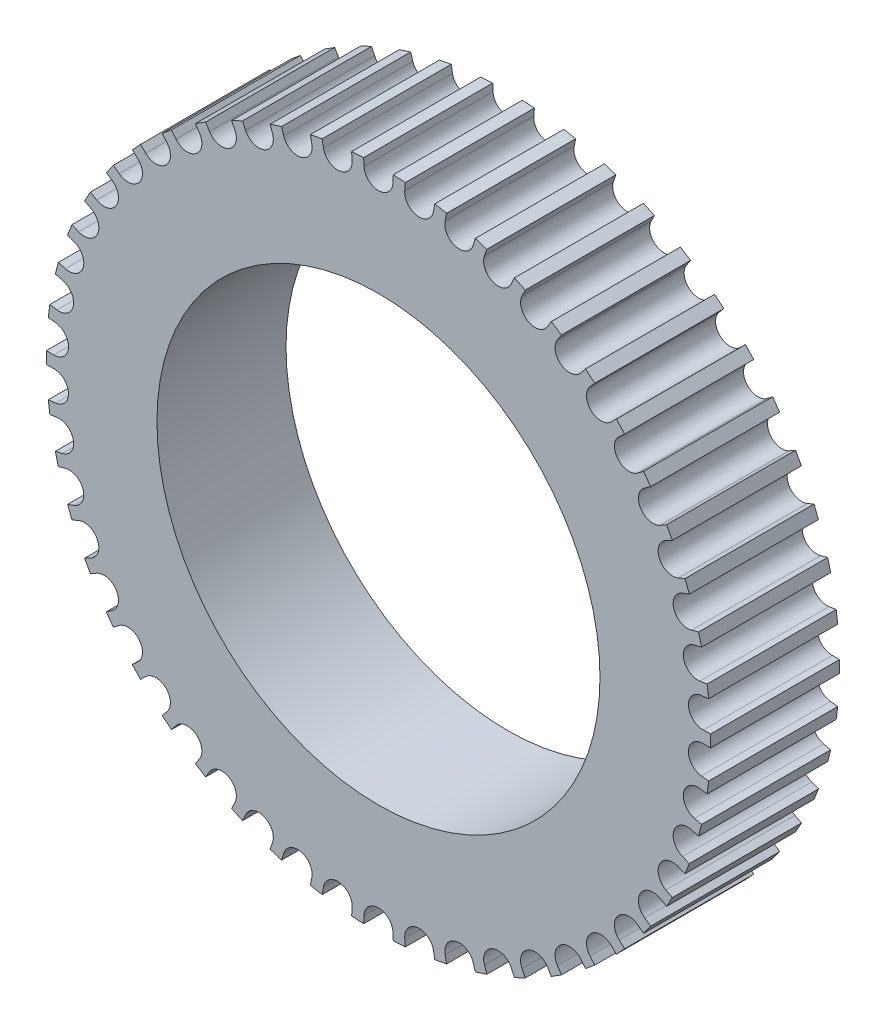
SolidWorks part; units mm, degrees
ref_plane "Front" through (0, 0, 0) normal (0, 0, 1) x (1, 0, 0)
ref_plane "Top" through (0, 0, 0) normal (0, 1, 0) x (1, 0, 0)
ref_plane "Right" through (0, 0, 0) normal (1, 0, 0) x (0, 0, -1)
sketch "Sketch1" plane through (0, 0, 0) normal (0, 0, 1) x (1, 0, 0)
  line L30 (-0.6744, -15.0836) -> (-0.6892, -15.4226)
  line L31 (0.6744, -15.0836) -> (0.6892, -15.4226)
  line L32 (0, -14.438) -> (0, -15.438) construction
  line L33 (-0.6892, -15.4226) -> (-1.2492, -15.3874)
  line L34 (-2.5595, -14.8801) -> (-2.6167, -15.2147)
  line L35 (-1.2214, -15.0492) -> (-1.2492, -15.3874)
  line L36 (-2.6167, -15.2147) -> (-3.1679, -15.1095)
  line L37 (-1.8096, -14.3242) -> (-1.9349, -15.3163) construction
  line L38 (-4.4043, -14.442) -> (-4.503, -14.7667)
  line L39 (-3.098, -14.7774) -> (-3.1679, -15.1095)
  line L40 (-4.503, -14.7667) -> (-5.0367, -14.5933)
  line L41 (-3.5906, -13.9844) -> (-3.8393, -14.953) construction
  line L42 (-6.1796, -13.7761) -> (-6.3182, -14.0859)
  line L43 (-4.9256, -14.2726) -> (-5.0367, -14.5933)
  line L44 (-6.3182, -14.0859) -> (-6.826, -13.847)
  line L45 (-5.315, -13.4241) -> (-5.6831, -14.3539) construction
  line L46 (-7.8575, -12.893) -> (-8.0338, -13.183)
  line L47 (-6.6756, -13.5427) -> (-6.826, -13.847)
  line L48 (-8.0338, -13.183) -> (-8.5077, -12.8823)
  line L49 (-6.9556, -12.6521) -> (-7.4373, -13.5284) construction
  line L50 (-9.4115, -11.8065) -> (-9.6227, -12.0721)
  line L51 (-8.3203, -12.5993) -> (-8.5077, -12.8823)
  line L52 (-9.6227, -12.0721) -> (-10.0551, -11.7144)
  line L53 (-8.4865, -11.6806) -> (-9.0742, -12.4896) construction
  line L54 (-10.817, -10.5338) -> (-11.0599, -10.7709)
  line L55 (-9.8338, -11.4571) -> (-10.0551, -11.7144)
  line L56 (-11.0599, -10.7709) -> (-11.4441, -10.3618)
  line L57 (-9.8835, -10.5249) -> (-10.5681, -11.2538) construction
  line L58 (-12.052, -9.095) -> (-12.3226, -9.2998)
  line L59 (-11.1923, -10.1342) -> (-11.4441, -10.3618)
  line L60 (-12.3226, -9.2998) -> (-12.6525, -8.8457)
  line L61 (-11.1247, -9.2031) -> (-11.8952, -9.8406) construction
  line L62 (-13.0968, -7.5128) -> (-13.391, -7.682)
  line L63 (-12.3742, -8.6516) -> (-12.6525, -8.8457)
  line L64 (-13.391, -7.682) -> (-13.6614, -7.1902)
  line L65 (-12.1904, -7.7363) -> (-13.0348, -8.2721) construction
  line L66 (-13.9352, -5.8121) -> (-14.2483, -5.9431)
  line L67 (-13.3609, -7.0325) -> (-13.6614, -7.1902)
  line L68 (-14.2483, -5.9431) -> (-14.4548, -5.4213)
  line L69 (-13.0639, -6.1474) -> (-13.9687, -6.5732) construction
  line L70 (-14.5537, -4.0197) -> (-14.8808, -4.1104)
  line L71 (-14.137, -5.3024) -> (-14.4548, -5.4213)
  line L72 (-14.8808, -4.1104) -> (-15.0203, -3.5669)
  line L73 (-13.7314, -4.4616) -> (-14.6824, -4.7706) construction
  line L74 (-14.9428, -2.164) -> (-15.2786, -2.213)
  line L75 (-14.6901, -3.4888) -> (-15.0203, -3.5669)
  line L76 (-15.2786, -2.213) -> (-15.3489, -1.6562)
  line L77 (-14.1823, -2.7054) -> (-15.1646, -2.8928) construction
  line L78 (-15.0962, -0.2741) -> (-15.4355, -0.2806)
  line L79 (-15.0115, -1.6201) -> (-15.3489, -1.6562)
  line L80 (-15.4355, -0.2806) -> (-15.4355, 0.2806)
  line L81 (-14.4095, -0.9066) -> (-15.4076, -0.9694) construction
  line L82 (-15.0115, 1.6201) -> (-15.3489, 1.6562)
  line L83 (-15.0962, 0.2741) -> (-15.4355, 0.2806)
  line L84 (-15.3489, 1.6562) -> (-15.2786, 2.213)
  line L85 (-14.4095, 0.9066) -> (-15.4076, 0.9694) construction
  line L86 (-14.6901, 3.4888) -> (-15.0203, 3.5669)
  line L87 (-14.9428, 2.164) -> (-15.2786, 2.213)
  line L88 (-15.0203, 3.5669) -> (-14.8808, 4.1104)
  line L89 (-14.1823, 2.7054) -> (-15.1646, 2.8928) construction
  line L90 (-14.137, 5.3024) -> (-14.4548, 5.4213)
  line L91 (-14.5537, 4.0197) -> (-14.8808, 4.1104)
  line L92 (-14.4548, 5.4213) -> (-14.2483, 5.9431)
  line L93 (-13.7314, 4.4616) -> (-14.6824, 4.7706) construction
  line L94 (-13.3609, 7.0325) -> (-13.6614, 7.1902)
  line L95 (-13.9352, 5.8121) -> (-14.2483, 5.9431)
  line L96 (-13.6614, 7.1902) -> (-13.391, 7.682)
  line L97 (-13.0639, 6.1474) -> (-13.9687, 6.5732) construction
  line L98 (-12.3742, 8.6516) -> (-12.6525, 8.8457)
  line L99 (-13.0968, 7.5128) -> (-13.391, 7.682)
  line L100 (-12.6525, 8.8457) -> (-12.3226, 9.2998)
  line L101 (-12.1904, 7.7363) -> (-13.0348, 8.2721) construction
  line L102 (-11.1923, 10.1342) -> (-11.4441, 10.3618)
  line L103 (-12.052, 9.095) -> (-12.3226, 9.2998)
  line L104 (-11.4441, 10.3618) -> (-11.0599, 10.7709)
  line L105 (-11.1247, 9.2031) -> (-11.8952, 9.8406) construction
  line L106 (-9.8338, 11.4571) -> (-10.0551, 11.7144)
  line L107 (-10.817, 10.5338) -> (-11.0599, 10.7709)
  line L108 (-10.0551, 11.7144) -> (-9.6227, 12.0721)
  line L109 (-9.8835, 10.5249) -> (-10.5681, 11.2538) construction
  line L110 (-8.3203, 12.5993) -> (-8.5077, 12.8823)
  line L111 (-9.4115, 11.8065) -> (-9.6227, 12.0721)
  line L112 (-8.5077, 12.8823) -> (-8.0338, 13.183)
  line L113 (-8.4865, 11.6806) -> (-9.0742, 12.4896) construction
  line L114 (-6.6756, 13.5427) -> (-6.826, 13.847)
  line L115 (-7.8575, 12.893) -> (-8.0338, 13.183)
  line L116 (-6.826, 13.847) -> (-6.3182, 14.0859)
  line L117 (-6.9556, 12.6521) -> (-7.4373, 13.5284) construction
  line L118 (-4.9256, 14.2726) -> (-5.0367, 14.5933)
  line L119 (-6.1796, 13.7761) -> (-6.3182, 14.0859)
  line L120 (-5.0367, 14.5933) -> (-4.503, 14.7667)
  line L121 (-5.315, 13.4241) -> (-5.6831, 14.3539) construction
  line L122 (-3.098, 14.7774) -> (-3.1679, 15.1095)
  line L123 (-4.4043, 14.442) -> (-4.503, 14.7667)
  line L124 (-3.1679, 15.1095) -> (-2.6167, 15.2147)
  line L125 (-3.5906, 13.9844) -> (-3.8393, 14.953) construction
  line L126 (-1.2214, 15.0492) -> (-1.2492, 15.3874)
  line L127 (-2.5595, 14.8801) -> (-2.6167, 15.2147)
  line L128 (-1.2492, 15.3874) -> (-0.6892, 15.4226)
  line L129 (-1.8096, 14.3242) -> (-1.9349, 15.3163) construction
  line L130 (0.6744, 15.0836) -> (0.6892, 15.4226)
  line L131 (-0.6744, 15.0836) -> (-0.6892, 15.4226)
  line L132 (0.6892, 15.4226) -> (1.2492, 15.3874)
  line L133 (0, 14.438) -> (0, 15.438) construction
  line L134 (2.5595, 14.8801) -> (2.6167, 15.2147)
  line L135 (1.2214, 15.0492) -> (1.2492, 15.3874)
  line L136 (2.6167, 15.2147) -> (3.1679, 15.1095)
  line L137 (1.8096, 14.3242) -> (1.9349, 15.3163) construction
  line L138 (4.4043, 14.442) -> (4.503, 14.7667)
  line L139 (3.098, 14.7774) -> (3.1679, 15.1095)
  line L140 (4.503, 14.7667) -> (5.0367, 14.5933)
  line L141 (3.5906, 13.9844) -> (3.8393, 14.953) construction
  line L142 (6.1796, 13.7761) -> (6.3182, 14.0859)
  line L143 (4.9256, 14.2726) -> (5.0367, 14.5933)
  line L144 (6.3182, 14.0859) -> (6.826, 13.847)
  line L145 (5.315, 13.4241) -> (5.6831, 14.3539) construction
  line L146 (7.8575, 12.893) -> (8.0338, 13.183)
  line L147 (6.6756, 13.5427) -> (6.826, 13.847)
  line L148 (8.0338, 13.183) -> (8.5077, 12.8823)
  line L149 (6.9556, 12.6521) -> (7.4373, 13.5284) construction
  line L150 (0, 0) -> (0, -14.438) construction
  line L151 (9.4115, 11.8065) -> (9.6227, 12.0721)
  line L152 (8.3203, 12.5993) -> (8.5077, 12.8823)
  line L153 (9.6227, 12.0721) -> (10.0551, 11.7144)
  line L154 (8.4865, 11.6806) -> (9.0742, 12.4896) construction
  line L155 (10.817, 10.5338) -> (11.0599, 10.7709)
  line L156 (9.8338, 11.4571) -> (10.0551, 11.7144)
  line L157 (11.0599, 10.7709) -> (11.4441, 10.3618)
  line L158 (9.8835, 10.5249) -> (10.5681, 11.2538) construction
  line L159 (12.052, 9.095) -> (12.3226, 9.2998)
  line L160 (11.1923, 10.1342) -> (11.4441, 10.3618)
  line L161 (12.3226, 9.2998) -> (12.6525, 8.8457)
  line L162 (11.1247, 9.2031) -> (11.8952, 9.8406) construction
  line L163 (13.0968, 7.5128) -> (13.391, 7.682)
  line L164 (12.3742, 8.6516) -> (12.6525, 8.8457)
  line L165 (13.391, 7.682) -> (13.6614, 7.1902)
  line L166 (12.1904, 7.7363) -> (13.0348, 8.2721) construction
  line L167 (13.9352, 5.8121) -> (14.2483, 5.9431)
  line L168 (13.3609, 7.0325) -> (13.6614, 7.1902)
  line L169 (14.2483, 5.9431) -> (14.4548, 5.4213)
  line L170 (13.0639, 6.1474) -> (13.9687, 6.5732) construction
  line L171 (14.5537, 4.0197) -> (14.8808, 4.1104)
  line L172 (14.137, 5.3024) -> (14.4548, 5.4213)
  line L173 (14.8808, 4.1104) -> (15.0203, 3.5669)
  line L174 (13.7314, 4.4616) -> (14.6824, 4.7706) construction
  line L175 (14.9428, 2.164) -> (15.2786, 2.213)
  line L176 (14.6901, 3.4888) -> (15.0203, 3.5669)
  line L177 (15.2786, 2.213) -> (15.3489, 1.6562)
  line L178 (14.1823, 2.7054) -> (15.1646, 2.8928) construction
  line L179 (15.0962, 0.2741) -> (15.4355, 0.2806)
  line L180 (15.0115, 1.6201) -> (15.3489, 1.6562)
  line L181 (15.4355, 0.2806) -> (15.4355, -0.2806)
  line L182 (14.4095, 0.9066) -> (15.4076, 0.9694) construction
  line L183 (15.0115, -1.6201) -> (15.3489, -1.6562)
  line L184 (15.0962, -0.2741) -> (15.4355, -0.2806)
  line L185 (15.3489, -1.6562) -> (15.2786, -2.213)
  line L186 (14.4095, -0.9066) -> (15.4076, -0.9694) construction
  line L187 (14.6901, -3.4888) -> (15.0203, -3.5669)
  line L188 (14.9428, -2.164) -> (15.2786, -2.213)
  line L189 (15.0203, -3.5669) -> (14.8808, -4.1104)
  line L190 (14.1823, -2.7054) -> (15.1646, -2.8928) construction
  line L191 (14.137, -5.3024) -> (14.4548, -5.4213)
  line L192 (14.5537, -4.0197) -> (14.8808, -4.1104)
  line L193 (14.4548, -5.4213) -> (14.2483, -5.9431)
  line L194 (13.7314, -4.4616) -> (14.6824, -4.7706) construction
  line L195 (13.3609, -7.0325) -> (13.6614, -7.1902)
  line L196 (13.9352, -5.8121) -> (14.2483, -5.9431)
  line L197 (13.6614, -7.1902) -> (13.391, -7.682)
  line L198 (13.0639, -6.1474) -> (13.9687, -6.5732) construction
  line L199 (12.3742, -8.6516) -> (12.6525, -8.8457)
  line L200 (13.0968, -7.5128) -> (13.391, -7.682)
  line L201 (12.6525, -8.8457) -> (12.3226, -9.2998)
  line L202 (12.1904, -7.7363) -> (13.0348, -8.2721) construction
  line L203 (11.1923, -10.1342) -> (11.4441, -10.3618)
  line L204 (12.052, -9.095) -> (12.3226, -9.2998)
  line L205 (11.4441, -10.3618) -> (11.0599, -10.7709)
  line L206 (11.1247, -9.2031) -> (11.8952, -9.8406) construction
  line L207 (9.8338, -11.4571) -> (10.0551, -11.7144)
  line L208 (10.817, -10.5338) -> (11.0599, -10.7709)
  line L209 (10.0551, -11.7144) -> (9.6227, -12.0721)
  line L210 (9.8835, -10.5249) -> (10.5681, -11.2538) construction
  line L211 (8.3203, -12.5993) -> (8.5077, -12.8823)
  line L212 (9.4115, -11.8065) -> (9.6227, -12.0721)
  line L213 (8.5077, -12.8823) -> (8.0338, -13.183)
  line L214 (8.4865, -11.6806) -> (9.0742, -12.4896) construction
  line L215 (6.6756, -13.5427) -> (6.826, -13.847)
  line L216 (7.8575, -12.893) -> (8.0338, -13.183)
  line L217 (6.826, -13.847) -> (6.3182, -14.0859)
  line L218 (6.9556, -12.6521) -> (7.4373, -13.5284) construction
  line L219 (4.9256, -14.2726) -> (5.0367, -14.5933)
  line L220 (6.1796, -13.7761) -> (6.3182, -14.0859)
  line L221 (5.0367, -14.5933) -> (4.503, -14.7667)
  line L222 (5.315, -13.4241) -> (5.6831, -14.3539) construction
  line L223 (3.098, -14.7774) -> (3.1679, -15.1095)
  line L224 (4.4043, -14.442) -> (4.503, -14.7667)
  line L225 (3.1679, -15.1095) -> (2.6167, -15.2147)
  line L226 (3.5906, -13.9844) -> (3.8393, -14.953) construction
  line L227 (1.2214, -15.0492) -> (1.2492, -15.3874)
  line L228 (2.5595, -14.8801) -> (2.6167, -15.2147)
  line L229 (1.2492, -15.3874) -> (0.6892, -15.4226)
  line L230 (1.8096, -14.3242) -> (1.9349, -15.3163) construction
  circle A31 centre (0, 0) radius 15.438 construction
  arc A32 (-0.6744, -15.0836) -> (0.6744, -15.0836) centre (0, -15.113) cw
  arc A33 (-2.5595, -14.8801) -> (-1.2214, -15.0492) centre (-1.8942, -14.9939) cw
  arc A34 (-4.4043, -14.442) -> (-3.098, -14.7774) centre (-3.7585, -14.6382) cw
  arc A35 (-6.1796, -13.7761) -> (-4.9256, -14.2726) centre (-5.5635, -14.0517) cw
  arc A36 (-7.8575, -12.893) -> (-6.6756, -13.5427) centre (-7.2808, -13.2436) cw
  arc A37 (-9.4115, -11.8065) -> (-8.3203, -12.5993) centre (-8.8832, -12.2267) cw
  arc A38 (-10.817, -10.5338) -> (-9.8338, -11.4571) centre (-10.3456, -11.0169) cw
  arc A39 (-12.052, -9.095) -> (-11.1923, -10.1342) centre (-11.6448, -9.6334) cw
  arc A40 (-13.0968, -7.5128) -> (-12.3742, -8.6516) centre (-12.7604, -8.098) cw
  arc A41 (-13.9352, -5.8121) -> (-13.3609, -7.0325) centre (-13.6747, -6.4348) cw
  arc A42 (-14.5537, -4.0197) -> (-14.137, -5.3024) centre (-14.3733, -4.6702) cw
  arc A43 (-14.9428, -2.164) -> (-14.6901, -3.4888) centre (-14.8453, -2.8319) cw
  arc A44 (-15.0962, -0.2741) -> (-15.0115, -1.6201) centre (-15.0832, -0.949) cw
  arc A45 (-15.0115, 1.6201) -> (-15.0962, 0.2741) centre (-15.0832, 0.949) cw
  arc A46 (-14.6901, 3.4888) -> (-14.9428, 2.164) centre (-14.8453, 2.8319) cw
  arc A47 (-14.137, 5.3024) -> (-14.5537, 4.0197) centre (-14.3733, 4.6702) cw
  arc A48 (-13.3609, 7.0325) -> (-13.9352, 5.8121) centre (-13.6747, 6.4348) cw
  arc A49 (-12.3742, 8.6516) -> (-13.0968, 7.5128) centre (-12.7604, 8.098) cw
  arc A50 (-11.1923, 10.1342) -> (-12.052, 9.095) centre (-11.6448, 9.6334) cw
  arc A51 (-9.8338, 11.4571) -> (-10.817, 10.5338) centre (-10.3456, 11.0169) cw
  arc A52 (-8.3203, 12.5993) -> (-9.4115, 11.8065) centre (-8.8832, 12.2267) cw
  arc A53 (-6.6756, 13.5427) -> (-7.8575, 12.893) centre (-7.2808, 13.2436) cw
  arc A54 (-4.9256, 14.2726) -> (-6.1796, 13.7761) centre (-5.5635, 14.0517) cw
  arc A55 (-3.098, 14.7774) -> (-4.4043, 14.442) centre (-3.7585, 14.6382) cw
  arc A56 (-1.2214, 15.0492) -> (-2.5595, 14.8801) centre (-1.8942, 14.9939) cw
  arc A57 (0.6744, 15.0836) -> (-0.6744, 15.0836) centre (0, 15.113) cw
  arc A58 (2.5595, 14.8801) -> (1.2214, 15.0492) centre (1.8942, 14.9939) cw
  arc A59 (4.4043, 14.442) -> (3.098, 14.7774) centre (3.7585, 14.6382) cw
  arc A60 (6.1796, 13.7761) -> (4.9256, 14.2726) centre (5.5635, 14.0517) cw
  arc A61 (7.8575, 12.893) -> (6.6756, 13.5427) centre (7.2808, 13.2436) cw
  arc A62 (9.4115, 11.8065) -> (8.3203, 12.5993) centre (8.8832, 12.2267) cw
  arc A63 (10.817, 10.5338) -> (9.8338, 11.4571) centre (10.3456, 11.0169) cw
  arc A64 (12.052, 9.095) -> (11.1923, 10.1342) centre (11.6448, 9.6334) cw
  arc A65 (13.0968, 7.5128) -> (12.3742, 8.6516) centre (12.7604, 8.098) cw
  arc A66 (13.9352, 5.8121) -> (13.3609, 7.0325) centre (13.6747, 6.4348) cw
  arc A73 (-1.9349, -15.3163) -> (0, -15.438) centre (0, 0) ccw construction
  arc A74 (14.5537, 4.0197) -> (14.137, 5.3024) centre (14.3733, 4.6702) cw
  arc A75 (14.9428, 2.164) -> (14.6901, 3.4888) centre (14.8453, 2.8319) cw
  arc A76 (15.0962, 0.2741) -> (15.0115, 1.6201) centre (15.0832, 0.949) cw
  arc A77 (15.0115, -1.6201) -> (15.0962, -0.2741) centre (15.0832, -0.949) cw
  arc A78 (14.6901, -3.4888) -> (14.9428, -2.164) centre (14.8453, -2.8319) cw
  arc A79 (14.137, -5.3024) -> (14.5537, -4.0197) centre (14.3733, -4.6702) cw
  arc A80 (13.3609, -7.0325) -> (13.9352, -5.8121) centre (13.6747, -6.4348) cw
  arc A81 (12.3742, -8.6516) -> (13.0968, -7.5128) centre (12.7604, -8.098) cw
  arc A82 (11.1923, -10.1342) -> (12.052, -9.095) centre (11.6448, -9.6334) cw
  arc A83 (9.8338, -11.4571) -> (10.817, -10.5338) centre (10.3456, -11.0169) cw
  arc A84 (8.3203, -12.5993) -> (9.4115, -11.8065) centre (8.8832, -12.2267) cw
  arc A85 (6.6756, -13.5427) -> (7.8575, -12.893) centre (7.2808, -13.2436) cw
  arc A86 (4.9256, -14.2726) -> (6.1796, -13.7761) centre (5.5635, -14.0517) cw
  arc A87 (3.098, -14.7774) -> (4.4043, -14.442) centre (3.7585, -14.6382) cw
  arc A88 (1.2214, -15.0492) -> (2.5595, -14.8801) centre (1.8942, -14.9939) cw
  dimension "D1" = 0.675
  dimension "D2" = 1
  dimension "D3" = 5
  dimension "D6" = 1.94
  dimension "D5" = 50
extrude "Boss-Extrude1" add sketch "Sketch1" along normal blind 6 contours L227 A88 L228 L225 L223 A87 L224 L221 L219 A86 L220 L217 L215 A85 L216 L213 L211 A84 L212 L209 L207 A83 L208 L205 L203 A82 L204 L201 L199 A81 L200 L197 L195 A80 L196 L193 L191 A79 L192 L189 L187 A78 L188 L185 L183 A77 L184 L181 L179 A76 L180
sketch "Sketch3" plane through (0, 0, 0) normal (0, 0, -1) x (-1, 0, 0)
  circle A0 centre (0, 0) radius 7.5
  dimension "D1" = 15
extrude "Boss-Extrude2" add sketch "Sketch3" along normal blind 5
sketch "Sketch4" plane through (0, 0, -5) normal (0, 0, -1) x (-1, 0, 0)
  circle A0 centre (0, 0) radius 2.55
  dimension "D1" = 5.1
extrude "Cut-Extrude1" cut sketch "Sketch4" against normal through all
sketch "Sketch6" plane through (0, 0, 0) normal (1, 0, 0) x (0, 0, -1)
  line L0 (5, -7.5) -> (5, 7.5) construction
  circle A0 centre (2.5, 0) radius 1.25
  dimension "D1" = 2.5
  dimension "D2" = 2.5
extrude "Cut-Extrude2" cut sketch "Sketch6" against normal through all both and the other way through all
sketch "Sketch7" plane through (0, 0, 6) normal (0, 0, 1) x (1, 0, 0)
  line L0 (-0.6744, -15.0836) -> (-0.6892, -15.4226) construction
  line L1 (-0.6744, -15.0836) -> (0.6744, -15.0836)
  line L2 (-0.6744, -15.0836) -> (-0.6462, -14.438)
  line L3 (-0.6462, -14.438) -> (0.6462, -14.438)
  line L4 (0.6744, -15.0836) -> (0.6462, -14.438)
  line L5 (0, -14.438) -> (0, -15.0836) construction
  line L6 (-0.6603, -14.7608) -> (0.6603, -14.7608) construction
  arc A0 (0.6744, -15.0836) -> (-0.6744, -15.0836) centre (0, -15.113) ccw construction
  point P296 (0, -14.7608)
extrude "Cut-Extrude3" [suppressed] cut sketch "Sketch7" against normal through all
pattern_circular "CirPattern1" [suppressed] count 50 over 360
fillet "Fillet1" [suppressed] radius 0.3
sketch "Sketch8" plane through (0, 0, -5) normal (0, 0, -1) x (-1, 0, 0)
  circle A0 centre (0, 0) radius 10.2976
extrude "Cut-Extrude4" cut sketch "Sketch8" against normal through all
